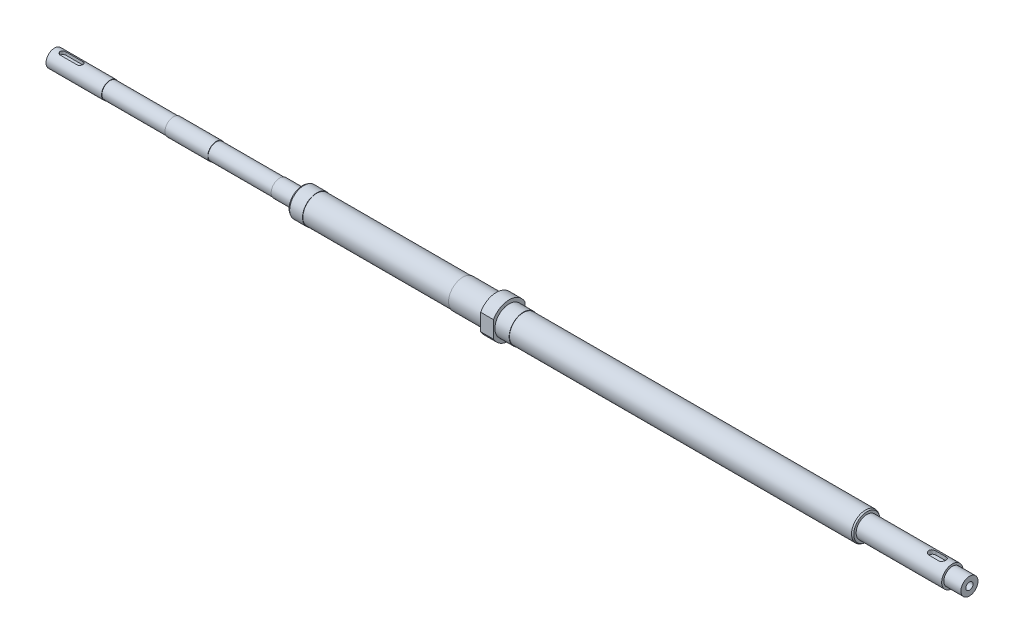
SolidWorks part; units mm, degrees
material "15 142   (42CrMo4)"
ref_plane "Přední rovina" through (0, 0, 0) normal (0, 0, 1) x (1, 0, 0)
ref_plane "Horní rovina" through (0, 0, 0) normal (0, 1, 0) x (1, 0, 0)
ref_plane "Pravá rovina" through (0, 0, 0) normal (1, 0, 0) x (0, 0, -1)
sketch "Skica1" plane through (0, 0, 0) normal (0, 0, 1) x (1, 0, 0)
  line L0 (-5427.2999, 0) -> (5427.2999, 0) construction
  line L1 (0, 0) -> (0, 6)
  line L2 (0, 6) -> (39, 6)
  line L3 (39, 6) -> (39, 5.75)
  line L4 (39, 5.75) -> (83.5, 5.75)
  line L5 (83.5, 5.75) -> (83.5, 6)
  line L6 (83.5, 6) -> (113.5, 6)
  line L7 (113.5, 6) -> (113.5, 5.75)
  line L8 (113.5, 5.75) -> (158, 5.75)
  line L9 (158, 5.75) -> (158, 6)
  line L10 (158, 6) -> (174, 6)
  line L11 (174, 6) -> (174, 10)
  line L12 (174, 10) -> (184, 10)
  line L13 (184, 10) -> (184, 9.75)
  line L14 (184, 9.75) -> (286.5, 9.75)
  line L15 (286.5, 9.75) -> (286.5, 10)
  line L16 (286.5, 10) -> (310, 10)
  line L17 (310, 10) -> (310, 12.5)
  line L18 (310, 12.5) -> (319, 12.5)
  line L19 (319, 12.5) -> (319, 10)
  line L20 (319, 10) -> (329, 10)
  line L21 (329, 10) -> (329, 9.75)
  line L22 (329, 9.75) -> (570, 9.75)
  line L23 (570, 9.75) -> (570, 7.5)
  line L24 (570, 7.5) -> (630, 7.5)
  line L25 (630, 7.5) -> (630, 6)
  line L26 (630, 6) -> (642, 6)
  line L27 (642, 6) -> (642, 0)
  line L28 (642, 0) -> (0, 0)
  point P4 (0, 0)
  dimension "D1" = 39
  dimension "D2" = 44.5
  dimension "D3" = 30
  dimension "D4" = 12
  dimension "D5" = 11.5
  dimension "D6" = 44.5
  dimension "D7" = 16
  dimension "D8" = 174
  dimension "D9" = 113.5
  dimension "D10" = 60.5
  dimension "D11" = 10
  dimension "D12" = 23.5
  dimension "D13" = 136
  dimension "D14" = 20
  dimension "D15" = 19.5
  dimension "D16" = 9
  dimension "D17" = 25
  dimension "D18" = 10
  dimension "D19" = 570
  dimension "D20" = 15
  dimension "D21" = 12
  dimension "D22" = 72
  dimension "D23" = 60
  dimension "D24" = 12
  dimension "D25" = 642
revolve "Rotovat1" add sketch "Skica1" angle 360 about L0
ref_plane "Rovina1" through (0, 6, 0) normal (0, 1, 0) x (1, 0, 0)
sketch "Skica2" plane through (0, 6, 0) normal (0, 1, 0) x (1, 0, 0)
  line L0 (6, 0) -> (18, 0) construction
  line L1 (-6.875, 0) -> (6.875, 0) construction
  line L2 (6, 2) -> (18, 2)
  line L3 (6, -2) -> (18, -2)
  line L4 (0, -55) -> (0, 55) construction
  arc A0 (6, 2) -> (6, -2) centre (6, 0) ccw
  arc A1 (18, -2) -> (18, 2) centre (18, 0) ccw
  point P5 (12, 0)
  dimension "D1" = 16
  dimension "D2" = 4
  dimension "D3" = 4
extrude "Odebrat vysunutím1" cut sketch "Skica2" against normal blind 2.4
ref_plane "Rovina2" through (0, 7.5, 0) normal (0, 1, 0) x (1, 0, 0)
sketch "Skica3" plane through (0, 7.5, 0) normal (0, 1, 0) x (1, 0, 0)
  line L0 (616, 0) -> (623, 0) construction
  line L1 (-6.875, 0) -> (6.875, 0) construction
  line L2 (616, 2.5) -> (623, 2.5)
  line L3 (616, -2.5) -> (623, -2.5)
  line L4 (630, -6) -> (630, 6) construction
  arc A0 (616, 2.5) -> (616, -2.5) centre (616, 0) ccw
  arc A1 (623, -2.5) -> (623, 2.5) centre (623, 0) ccw
  point P5 (619.5, 0)
  dimension "D1" = 12
  dimension "D2" = 4.5
  dimension "D3" = 5
extrude "Odebrat vysunutím2" cut sketch "Skica3" against normal blind 2.9
sketch "Skica4" plane through (319, 0, 0) normal (1, 0, 0) x (0, 0, -1)
  line L0 (0, 0) -> (0, 34.5316) construction
  line L1 (-11, 22.8372) -> (-54.2017, 22.8372)
  line L2 (-11, 22.8372) -> (-11, -34.1852)
  line L3 (-11, -34.1852) -> (-54.2017, -34.1852)
  line L4 (-54.2017, 22.8372) -> (-54.2017, -34.1852)
  line L5 (11, 27.0897) -> (39.7045, 27.0897)
  line L6 (11, 27.0897) -> (11, -35.4416)
  line L7 (11, -35.4416) -> (39.7045, -35.4416)
  line L8 (39.7045, 27.0897) -> (39.7045, -35.4416)
  line L9 (0, 6.875) -> (0, -6.875) construction
  dimension "D1" = 22
extrude "Odebrat vysunutím3" cut sketch "Skica4" against normal through all
hole_wizard "M6 závit1" positions "Skica5" profile "Skica6" tap size "M6" standard "DIN"
sketch "Skica5" plane through (642, 0, 0) normal (1, 0, 0) x (0, 0, -1)
  point P0 (0, 0)
sketch "Skica6" plane through (642, 0, 0) normal (0, 1, 0) x (0, 0, -1)
  line L0 (0, 0) -> (0, 23.5022)
  line L1 (0, 23.5022) -> (2.5, 22)
  line L2 (2.5, 22) -> (2.5, 0)
  line L5 (2.5, 0) -> (0, 0)
  line L10 (0, 23.5022) -> (-2.5, 22) construction
  line L11 (0, -6.35) -> (0, 107.95) construction
  dimension "Průměr závitníku" = 5
  dimension "Hloubka závitníku" = 22
  dimension "Úhel vrtání" = 118
cosmetic thread "Závit díry1" parameters "D1"=18, "D2"=6
hole_wizard "M5 závit1" positions "Skica7" profile "Skica8" tap size "M5" standard "DIN"
sketch "Skica7" plane through (0, 0, 0) normal (-1, 0, 0) x (0, 0, 1)
  point P0 (0, 0)
sketch "Skica8" plane through (0, 0, 0) normal (0, 1, 0) x (0, 0, 1)
  line L0 (0, 0) -> (0, 21.2618)
  line L1 (0, 21.2618) -> (2.1, 20)
  line L2 (2.1, 20) -> (2.1, 0)
  line L5 (2.1, 0) -> (0, 0)
  line L10 (0, 21.2618) -> (-2.1, 20) construction
  line L11 (0, -6.35) -> (0, 107.95) construction
  dimension "Průměr závitníku" = 4.2
  dimension "Hloubka závitníku" = 20
  dimension "Úhel vrtání" = 118
cosmetic thread "Závit díry2" parameters "D1"=16, "D2"=5
chamfer "Zkosení1" distance 1 angle 30 2 edges at (570, -9.75, 0) (174, -10, 0)
